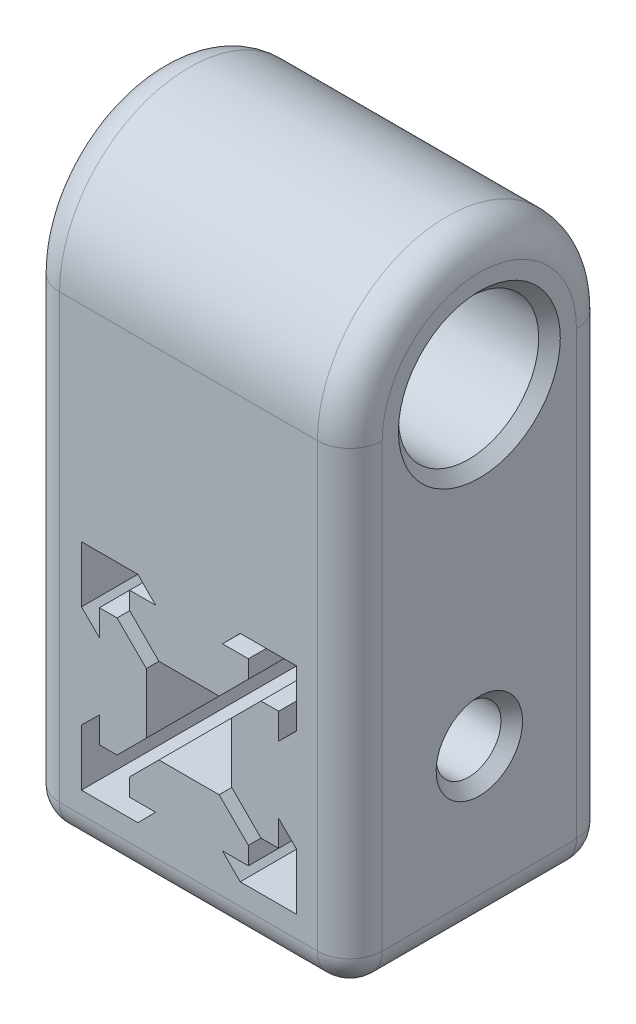
SolidWorks part; units mm, degrees
ref_plane "Front Plane" through (0, 0, 0) normal (0, 0, 1) x (1, 0, 0)
ref_plane "Top Plane" through (0, 0, 0) normal (0, 1, 0) x (1, 0, 0)
ref_plane "Right Plane" through (0, 0, 0) normal (1, 0, 0) x (0, 0, -1)
sketch "Sketch1" plane through (0, 0, 0) normal (0, 0, 1) x (1, 0, 0)
  line L0 (0, -15) -> (0, 15) construction
  line L1 (0, 15) -> (14.8993, 15)
  line L2 (14.8993, 15) -> (14.8993, -14.9496)
  line L3 (14.8993, -14.9496) -> (-15, -14.9496)
  line L4 (-15, -14.9496) -> (-15, 15)
  line L5 (-15, 15) -> (0, 15)
  line L6 (0, -9.9664) -> (0, 9.9664) construction
  line L7 (0, 9.9664) -> (-9.9664, 9.9664) construction
  line L8 (-9.9664, 9.9664) -> (-4.7414, 9.9664)
  line L9 (-4.7414, 9.9664) -> (-3.1, 8.3075)
  line L10 (-3.1, 8.3075) -> (0, 8.3075) construction
  line L11 (-3.1, 8.3075) -> (-5.5, 8.3075)
  line L12 (-5.5, 8.3075) -> (-5.5, 6.6675)
  line L13 (-5.5, 6.6675) -> (-2.79, 3.9575)
  line L14 (-2.79, 3.9575) -> (0, 3.9575) construction
  line L15 (-2.79, 3.9575) -> (2.79, 3.9575)
  line L16 (-9.9664, 9.9664) -> (0, 0) construction
  line L17 (-3.9575, 2.79) -> (-3.9575, -2.79)
  line L18 (-6.6675, 5.5) -> (-3.9575, 2.79)
  line L19 (-8.3075, 5.5) -> (-6.6675, 5.5)
  line L20 (-8.3075, 3.1) -> (-8.3075, 5.5)
  line L21 (-9.9664, 4.7414) -> (-8.3075, 3.1)
  line L22 (-9.9664, 9.9664) -> (-9.9664, 4.7414)
  line L23 (0, 0) -> (-11.0308, 0) construction
  line L24 (5.5, 6.6675) -> (2.79, 3.9575)
  line L25 (5.5, 8.3075) -> (5.5, 6.6675)
  line L26 (3.1, 8.3075) -> (5.5, 8.3075)
  line L27 (4.7414, 9.9664) -> (3.1, 8.3075)
  line L28 (9.9664, 9.9664) -> (4.7414, 9.9664)
  line L29 (9.9664, 9.9664) -> (9.9664, 4.7414)
  line L30 (9.9664, 4.7414) -> (8.3075, 3.1)
  line L31 (8.3075, 3.1) -> (8.3075, 5.5)
  line L32 (8.3075, 5.5) -> (6.6675, 5.5)
  line L33 (6.6675, 5.5) -> (3.9575, 2.79)
  line L34 (3.9575, 2.79) -> (3.9575, -2.79)
  line L35 (-9.9664, -9.9664) -> (0, 0) construction
  line L36 (-2.79, -3.9575) -> (0, -3.9575) construction
  line L37 (-3.1, -8.3075) -> (0, -8.3075) construction
  line L38 (0, -9.9664) -> (-9.9664, -9.9664) construction
  line L39 (6.6675, -5.5) -> (3.9575, -2.79)
  line L40 (8.3075, -5.5) -> (6.6675, -5.5)
  line L41 (8.3075, -3.1) -> (8.3075, -5.5)
  line L42 (9.9664, -4.7414) -> (8.3075, -3.1)
  line L43 (9.9664, -9.9664) -> (9.9664, -4.7414)
  line L44 (9.9664, -9.9664) -> (4.7414, -9.9664)
  line L45 (4.7414, -9.9664) -> (3.1, -8.3075)
  line L46 (3.1, -8.3075) -> (5.5, -8.3075)
  line L47 (5.5, -8.3075) -> (5.5, -6.6675)
  line L48 (5.5, -6.6675) -> (2.79, -3.9575)
  line L49 (-9.9664, -9.9664) -> (-9.9664, -4.7414)
  line L50 (-9.9664, -4.7414) -> (-8.3075, -3.1)
  line L51 (-8.3075, -3.1) -> (-8.3075, -5.5)
  line L52 (-8.3075, -5.5) -> (-6.6675, -5.5)
  line L53 (-6.6675, -5.5) -> (-3.9575, -2.79)
  line L54 (-2.79, -3.9575) -> (2.79, -3.9575)
  line L55 (-5.5, -6.6675) -> (-2.79, -3.9575)
  line L56 (-5.5, -8.3075) -> (-5.5, -6.6675)
  line L57 (-3.1, -8.3075) -> (-5.5, -8.3075)
  line L58 (-4.7414, -9.9664) -> (-3.1, -8.3075)
  line L59 (-9.9664, -9.9664) -> (-4.7414, -9.9664)
  point P43 (3.9575, 0)
  point P58 (-3.9575, 0)
  dimension "D1" = 3.1
  dimension "D2" = 2.79
  dimension "D3" = 2.4
  dimension "D4" = 135
  dimension "D5" = 1.64
  dimension "D6" = 15
  dimension "D7" = 15
  dimension "D8" = 9.9664
  dimension "D9" = 5.225
extrude "Boss-Extrude1" add sketch "Sketch1" along normal blind 24
sketch "Sketch5" plane through (-15, 0, 0) normal (-1, 0, 0) x (0, 0, 1)
  line L0 (0, 15) -> (0, 22.5)
  line L2 (0, 15) -> (24, 15)
  line L9 (24, 22.5) -> (24, 15)
  line L11 (12, 22.5) -> (12, 29) construction
  line L12 (0, 22.5) -> (0, 29)
  line L13 (24, 29) -> (24, 22.5)
  circle A2 centre (12, 29) radius 6.5
  arc A3 (0, 29) -> (24, 29) centre (12, 29) cw
  dimension "D1" = 7.5
  dimension "D2" = 24
extrude "Boss-Extrude3" add sketch "Sketch5" against normal through all
sketch "Sketch3" plane through (-15, 0, 0) normal (-1, 0, 0) x (0, 0, 1)
  line L0 (12, 0) -> (24, 7.0252) construction
  line L2 (0, 0) -> (12, 0) construction
  line L3 (24, 29) -> (24, -14.9496) construction
  circle A0 centre (12, 0) radius 3
extrude "Cut-Extrude1" cut sketch "Sketch3" against normal through all
fillet "Fillet1" radius 3 10 edges at (-0.0504, -14.9496, 0) (-0.0504, -14.9496, 24) (14.8993, 7.0252, 0) (14.8993, 7.0252, 24) (-15, 7.0252, 0) (-15, 7.0252, 24) (14.8993, -14.9496, 12) (-15, -14.9496, 12) (-15, 41, 12) (14.8993, 41, 12)
chamfer "Chamfer1" distance 1 angle 45 4 edges at (-15, 0, 15) (-15, 29, 18.5) (14.8993, 0, 15) (14.8993, 29, 18.5)
